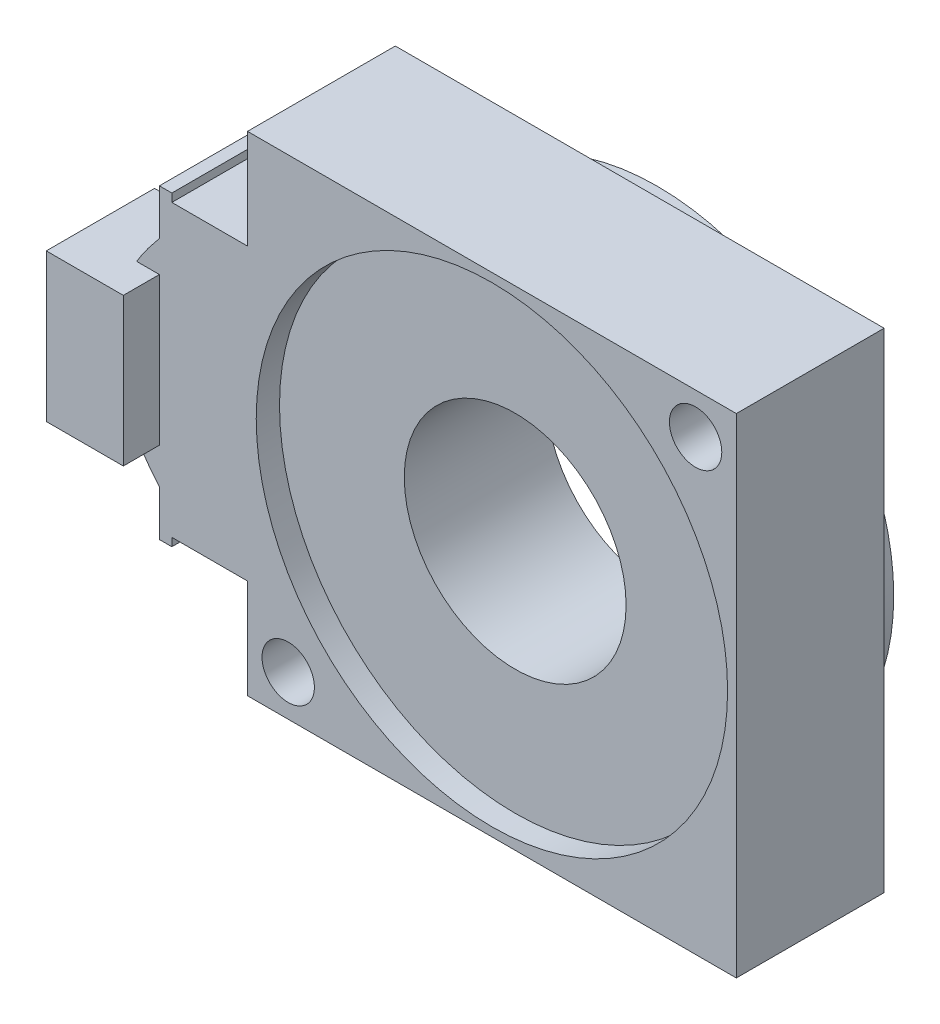
SolidWorks part; units mm, degrees
ref_plane "Front Plane" through (0, 0, 0) normal (0, 0, 1) x (1, 0, 0)
ref_plane "Top Plane" through (0, 0, 0) normal (0, 1, 0) x (1, 0, 0)
ref_plane "Right Plane" through (0, 0, 0) normal (1, 0, 0) x (0, 0, -1)
sketch "Sketch1" plane through (0, 0, 0) normal (0, 0, 1) x (1, 0, 0)
  line L0 (0, 0) -> (0, 21) construction
  line L1 (0, 21) -> (21, 21)
  line L2 (0, 21) -> (-21, 21)
  line L3 (21, 21) -> (21, -21)
  line L4 (21, -21) -> (-21, -21)
  line L5 (-21, 21) -> (-21, -21)
  dimension "D1" = 21
  dimension "D2" = 21
  dimension "D3" = 21
  dimension "D4" = 42
extrude "Boss-Extrude1" add sketch "Sketch1" along normal blind 12.7
sketch "Sketch2" plane through (0, 0, 0) normal (0, 0, 1) x (1, 0, 0)
  line L0 (0, 0) -> (17.5009, 17.5009) construction
  line L1 (0, 0) -> (-28.2843, 28.2843) construction
  circle A0 centre (17.5009, 17.5009) radius 2.25
  circle A1 centre (-17.5009, -17.5009) radius 2.25
  dimension "D3" = 4.5
  dimension "D1" = 24.75
  dimension "D2" = 40
extrude "Cut-Extrude1" cut sketch "Sketch2" along normal blind 12.7
sketch "Sketch3" plane through (0, 0, 12.7) normal (0, 0, 1) x (1, 0, 0)
  line L0 (-17.5009, -17.5009) -> (-21, -17.5009) construction
  line L1 (-21, 21) -> (-21, -21) construction
  line L2 (-21, -17.5009) -> (-21, -12.4609) construction
  line L3 (-21, -12.4609) -> (-27.5, -12.4609)
  line L4 (-27.5, -12.4609) -> (-27.5, -13.1609)
  line L5 (-27.5, -13.1609) -> (-28.57, -13.1609)
  line L6 (-28.57, -13.1609) -> (-28.57, -9.2409)
  line L7 (0, 0) -> (-40, 0) construction
  line L8 (-28.57, 13.1609) -> (-28.57, 9.2409)
  line L9 (-27.5, 12.4609) -> (-27.5, 13.1609)
  line L10 (-27.5, 13.1609) -> (-28.57, 13.1609)
  line L11 (-21, 12.4609) -> (-27.5, 12.4609)
  line L12 (-21, 12.4609) -> (-21, -12.4609)
  line L13 (0, 0) -> (-32.51, 0) construction
  spline S0 degree 2 poles (-28.57, 9.2409) (-36.45, 0) (-28.57, -9.2409) knots 0 0 0 1 1 1
  dimension "D1" = 3.4991
  dimension "D2" = 5.04
  dimension "D3" = 6.5
  dimension "D4" = 0.7
  dimension "D5" = 1.07
  dimension "D6" = 3.92
  dimension "D7" = 40
  dimension "D8" = 32.51
extrude "Boss-Extrude4" add sketch "Sketch3" against normal blind 12.7
sketch "Sketch4" plane through (0, 0, 12.7) normal (0, 0, 1) x (1, 0, 0)
  circle A0 centre (0, 0) radius 20.25
extrude "Cut-Extrude2" cut sketch "Sketch4" against normal blind 2
sketch "Sketch5" plane through (0, 0, 10.7) normal (0, 0, 1) x (1, 0, 0)
  circle A0 centre (0, 0) radius 9.53
  dimension "D1" = 19.06
sketch "Sketch6" plane through (0, 0, 0) normal (0, 0, -1) x (-1, 0, 0)
  circle A0 centre (0, 0) radius 20.325
  dimension "D1" = 40.65
extrude "Boss-Extrude5" add sketch "Sketch6" along normal blind 1.5
extrude "Cut-Extrude3" cut sketch "Sketch5" against normal blind 30
sketch "Sketch8" plane through (0, 0, 12.7) normal (0, 0, 1) x (1, 0, 0)
  line L0 (-28.57, 9.2409) -> (-28.57, 6.5609) construction
  line L1 (-28.57, 6.5609) -> (-35.19, 6.5609)
  line L2 (-35.19, 6.5609) -> (-35.19, -6.1391)
  line L3 (-35.19, -6.1391) -> (-28.57, -6.1391)
  line L4 (-28.57, -6.1391) -> (-28.57, 6.5609)
  dimension "D1" = 2.68
  dimension "D2" = 6.62
  dimension "D3" = 12.7
extrude "Boss-Extrude7" add sketch "Sketch8" against normal blind 6.2 and the other way blind 3.1
